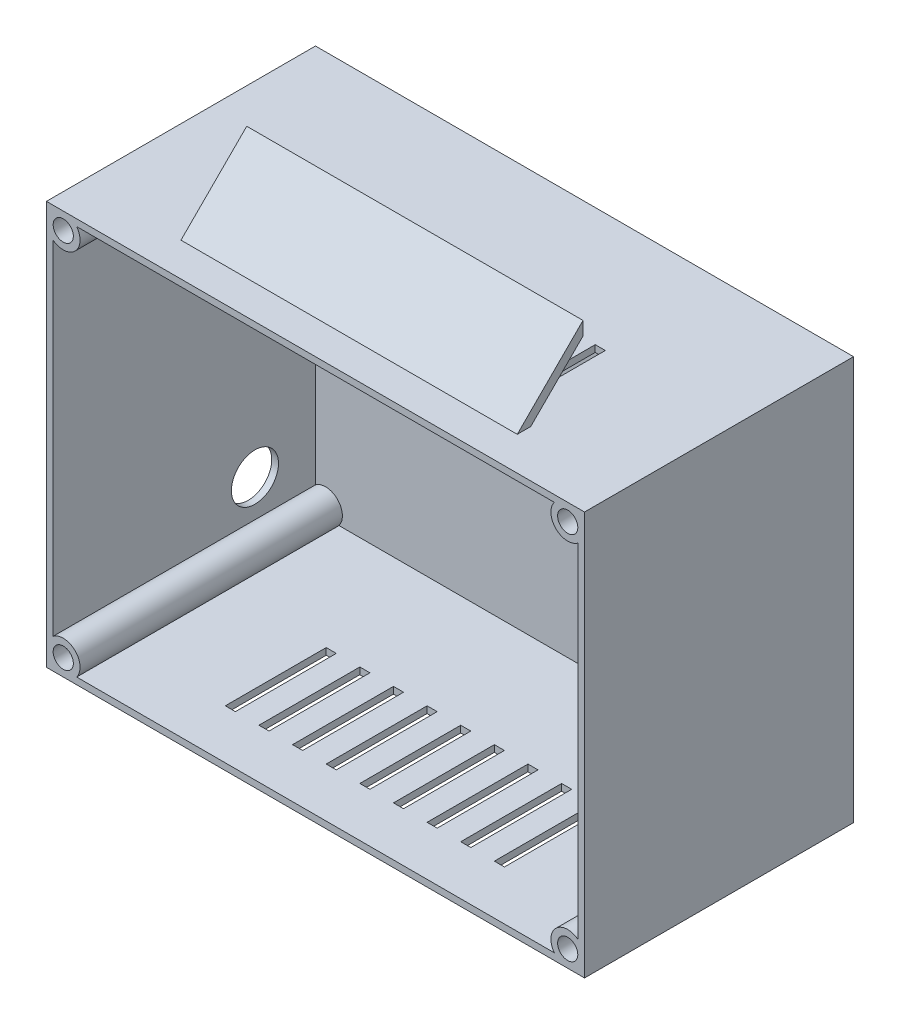
SolidWorks part; units mm, degrees
ref_plane "Alzado" through (0, 0, 0) normal (0, 0, 1) x (1, 0, 0)
ref_plane "Planta" through (0, 0, 0) normal (0, 1, 0) x (1, 0, 0)
ref_plane "Vista lateral" through (0, 0, 0) normal (1, 0, 0) x (0, 0, -1)
sketch "Croquis1" plane through (0, 0, 0) normal (0, 0, 1) x (1, 0, 0)
  line L1 (-40, -30) -> (40, -30)
  line L2 (-40, -30) -> (-40, 30)
  line L3 (-40, 30) -> (40, 30)
  line L4 (40, -30) -> (40, 30)
  line L5 (-40, -30) -> (40, 30) construction
  line L6 (-40, 30) -> (40, -30) construction
  point P0 (0, 0)
  dimension "D1" = 80
  dimension "D2" = 60
extrude "Saliente-Extruir1" add sketch "Croquis1" along normal blind 40
shell "Vaciado1" thickness 1
sketch "Croquis2" plane through (0, 0, 40) normal (0, 0, 1) x (1, 0, 0)
  line L0 (-39, 29) -> (-37.5, 29) construction
  line L1 (39, 29) -> (-39, 29) construction
  line L2 (-37.5, 29) -> (-37.5, 27.5) construction
  line L3 (0, -39.3201) -> (0, 35.1664) construction
  line L4 (-36.1396, 0) -> (45.5978, 0) construction
  circle A0 centre (-37.5, 27.5) radius 1.5
  circle A1 centre (-37.5, 27.5) radius 2.5
  circle A2 centre (37.5, 27.5) radius 2.5
  circle A3 centre (37.5, 27.5) radius 1.5
  circle A4 centre (37.5, -27.5) radius 2.5
  circle A5 centre (37.5, -27.5) radius 1.5
  circle A6 centre (-37.5, -27.5) radius 1.5
  circle A7 centre (-37.5, -27.5) radius 2.5
  dimension "D1" = 1.5
  dimension "D2" = 1.5
extrude "Saliente-Extruir2" add sketch "Croquis2" against normal blind 40
sketch "Croquis3" plane through (0, 0, 0) normal (1, 0, 0) x (0, 0, -1)
  line L0 (0, 0) -> (-35, 0) construction
  line L3 (-35, 0) -> (-35, -30) construction
  line L4 (-40, -30) -> (0, -30) construction
  line L5 (-35, -30) -> (-25.2216, -39.7784)
  line L6 (-25.2216, -39.7784) -> (-25.2216, -37.7784)
  line L7 (-25.2216, -37.7784) -> (-33.2245, -29.7755)
  line L8 (-33.2245, -29.7755) -> (-35, -29.7755)
  line L9 (-35, -29.7755) -> (-35, -30)
  dimension "D1" = 35
  dimension "D2" = 2
extrude "Saliente-Extruir3" add sketch "Croquis3" along normal mid plane 50
mirror "Simetría1" about plane through (0, 0, 0) normal (0, 1, 0) of "Saliente-Extruir3"
sketch "Croquis4" plane through (0, 30, 0) normal (0, 1, 0) x (1, 0, 0)
  line L0 (0, -40) -> (0, 0) construction
  line L1 (40, -40) -> (-40, -40) construction
  line L2 (4.25, -17.6576) -> (4.25, -32.6576)
  line L3 (-0.75, -17.6576) -> (0.75, -17.6576)
  line L4 (-0.75, -17.6576) -> (-0.75, -32.6576)
  line L5 (-0.75, -32.6576) -> (0.75, -32.6576)
  line L6 (0.75, -17.6576) -> (0.75, -32.6576)
  line L7 (-0.75, -17.6576) -> (0.75, -32.6576) construction
  line L8 (-0.75, -32.6576) -> (0.75, -17.6576) construction
  line L9 (4.25, -17.6576) -> (5.75, -17.6576)
  line L10 (5.75, -17.6576) -> (5.75, -32.6576)
  line L11 (4.25, -32.6576) -> (5.75, -32.6576)
  line L12 (9.25, -17.6576) -> (9.25, -32.6576)
  line L13 (9.25, -17.6576) -> (10.75, -17.6576)
  line L14 (10.75, -17.6576) -> (10.75, -32.6576)
  line L15 (9.25, -32.6576) -> (10.75, -32.6576)
  line L16 (14.25, -17.6576) -> (14.25, -32.6576)
  line L17 (14.25, -17.6576) -> (15.75, -17.6576)
  line L18 (15.75, -17.6576) -> (15.75, -32.6576)
  line L19 (14.25, -32.6576) -> (15.75, -32.6576)
  line L20 (19.25, -17.6576) -> (19.25, -32.6576)
  line L21 (19.25, -17.6576) -> (20.75, -17.6576)
  line L22 (20.75, -17.6576) -> (20.75, -32.6576)
  line L23 (19.25, -32.6576) -> (20.75, -32.6576)
  line L24 (-5.75, -17.6576) -> (-5.75, -32.6576)
  line L25 (-5.75, -17.6576) -> (-4.25, -17.6576)
  line L26 (-4.25, -17.6576) -> (-4.25, -32.6576)
  line L27 (-5.75, -32.6576) -> (-4.25, -32.6576)
  line L28 (-10.75, -17.6576) -> (-10.75, -32.6576)
  line L29 (-10.75, -17.6576) -> (-9.25, -17.6576)
  line L30 (-9.25, -17.6576) -> (-9.25, -32.6576)
  line L31 (-10.75, -32.6576) -> (-9.25, -32.6576)
  line L32 (-15.75, -17.6576) -> (-15.75, -32.6576)
  line L33 (-15.75, -17.6576) -> (-14.25, -17.6576)
  line L34 (-14.25, -17.6576) -> (-14.25, -32.6576)
  line L35 (-15.75, -32.6576) -> (-14.25, -32.6576)
  line L36 (-20.75, -17.6576) -> (-20.75, -32.6576)
  line L37 (-20.75, -17.6576) -> (-19.25, -17.6576)
  line L38 (-19.25, -17.6576) -> (-19.25, -32.6576)
  line L39 (-20.75, -32.6576) -> (-19.25, -32.6576)
  point P5 (0, -25.1576)
  dimension "D1" = 15
  dimension "D2" = 1.5
  dimension "D3" = 5
  dimension "D4" = 5
extrude "Cortar-Extruir1" cut sketch "Croquis4" against normal up to next (1 mm away)
mirror "Simetría2" about plane through (0, 0, 0) normal (0, 1, 0) of "Cortar-Extruir1"
sketch "Croquis5" plane through (0, 0, 1) normal (0, 0, 1) x (1, 0, 0)
  circle A0 centre (37.5, -27.5) radius 1.5
  circle A1 centre (37.5, 27.5) radius 1.5
  circle A2 centre (-37.5, 27.5) radius 1.5
  circle A3 centre (-37.5, -27.5) radius 1.5
extrude "Saliente-Extruir4" add sketch "Croquis5" along normal blind 35
sketch "Croquis6" plane through (-40, 0, 0) normal (-1, 0, 0) x (0, 0, 1)
  line L0 (0, -30) -> (0, -20) construction
  line L1 (0, 30) -> (0, -30) construction
  line L2 (0, -20) -> (10, -20) construction
  circle A0 centre (10, -20) radius 3.5
  dimension "D3" = 7
  dimension "D1" = 10
  dimension "D2" = 10
extrude "Cortar-Extruir2" cut sketch "Croquis6" against normal up to next
